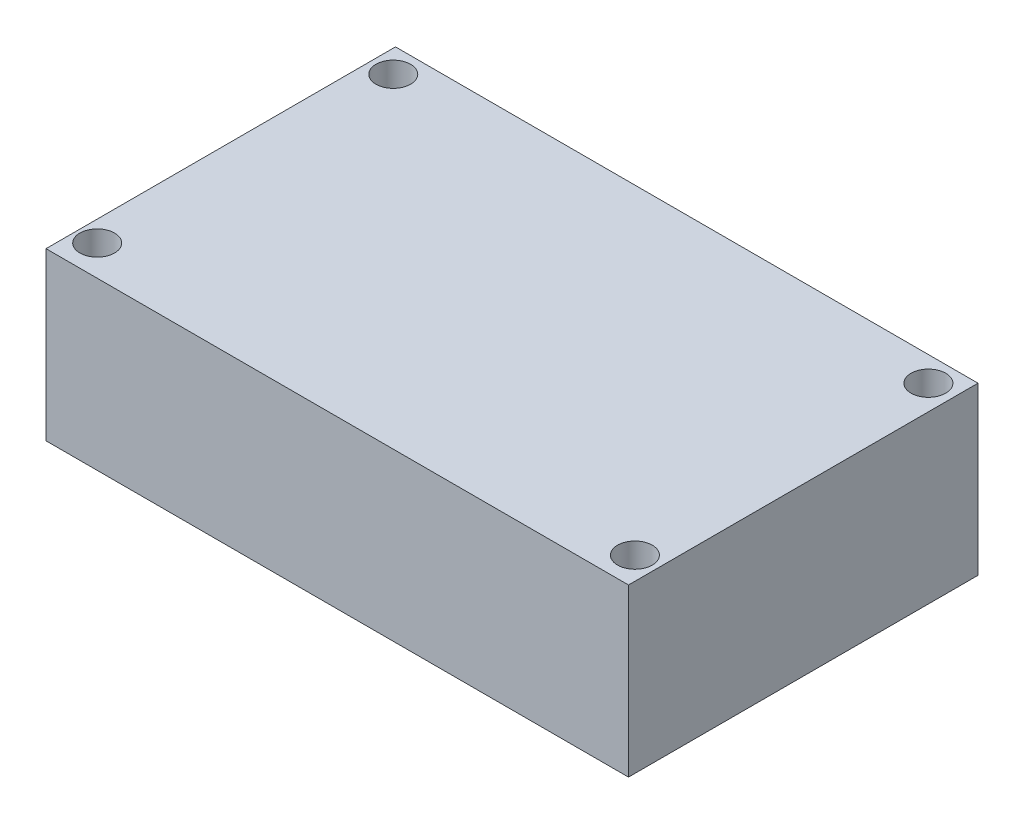
SolidWorks part; units mm, degrees
ref_plane "Płaszczyzna przednia" through (0, 0, 0) normal (0, 0, 1) x (1, 0, 0)
ref_plane "Płaszczyzna górna" through (0, 0, 0) normal (0, 1, 0) x (1, 0, 0)
ref_plane "Płaszczyzna prawa" through (0, 0, 0) normal (1, 0, 0) x (0, 0, -1)
sketch "Sketch1" plane through (0, 0, 0) normal (0, 1, 0) x (1, 0, 0)
  line L1 (-21, -12.6) -> (21, -12.6)
  line L2 (-21, -12.6) -> (-21, 12.6)
  line L3 (-21, 12.6) -> (21, 12.6)
  line L4 (21, -12.6) -> (21, 12.6)
  line L5 (-21, -12.6) -> (21, 12.6) construction
  line L6 (-21, 12.6) -> (21, -12.6) construction
  point P0 (0, 0)
  dimension "D1" = 42
  dimension "D2" = 25.2
extrude "Boss-Extrude1" add sketch "Sketch1" along normal blind 12
sketch "Sketch2" plane through (0, 12, 0) normal (0, 1, 0) x (1, 0, 0)
  circle A0 centre (-19.3712, 10.8096) radius 1.25
  circle A1 centre (-19.5048, -10.4032) radius 1.25
  circle A2 centre (19.3682, -10.507) radius 1.25
  circle A3 centre (19.2138, 10.8096) radius 1.25
  point P8 (19.2138, 10.8096)
extrude "Cut-Extrude1" cut sketch "Sketch2" against normal blind 20
